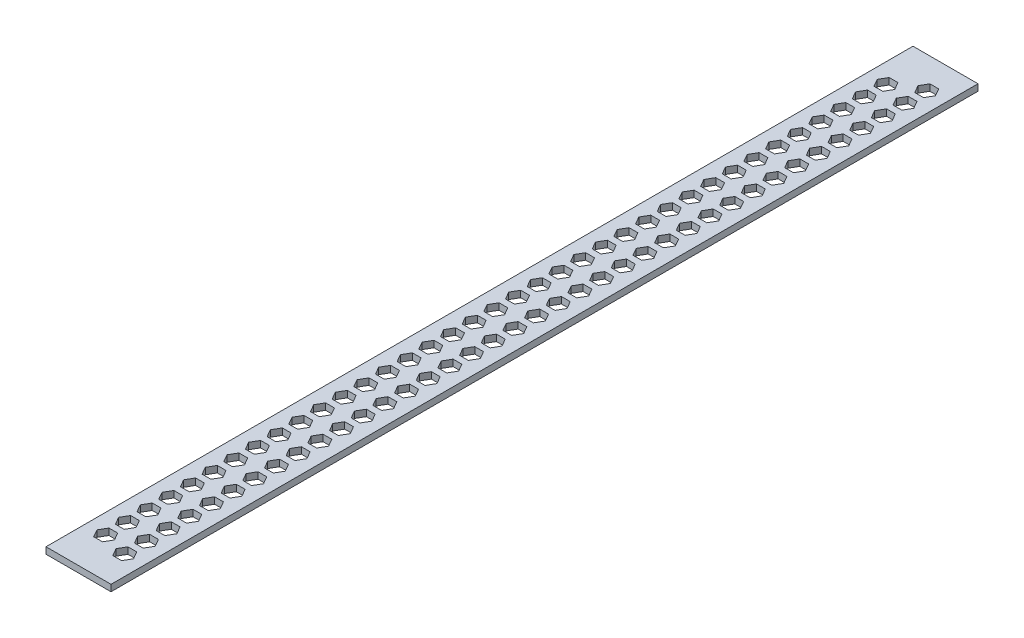
SolidWorks part; units mm, degrees
material "Balsa"
ref_plane "Front Plane" through (0, 0, 0) normal (0, 0, 1) x (1, 0, 0)
ref_plane "Top Plane" through (0, 0, 0) normal (0, 1, 0) x (1, 0, 0)
ref_plane "Right Plane" through (0, 0, 0) normal (1, 0, 0) x (0, 0, -1)
sketch "Sketch1" plane through (0, 0, 0) normal (0, 1, 0) x (1, 0, 0)
  line L1 (-36.5161, 312.7563) -> (-6.5161, 312.7563)
  line L2 (-36.5161, 312.7563) -> (-36.5161, -87.2437)
  line L3 (-36.5161, -87.2437) -> (-6.5161, -87.2437)
  line L4 (-6.5161, 312.7563) -> (-6.5161, -87.2437)
  line L5 (-36.5161, 312.7563) -> (-6.5161, -87.2437) construction
  line L6 (-36.5161, -87.2437) -> (-6.5161, 312.7563) construction
  point P0 (-21.5161, 112.7563)
  dimension "D1" = 400
  dimension "D2" = 30
extrude "Boss-Extrude1" add sketch "Sketch1" along normal blind 3
sketch "Sketch2" plane through (0, 0, 0) normal (0, -1, 0) x (-1, 0, 0)
  line L8 (11.5161, -71.8634) -> (13.5369, -75.3634)
  line L9 (13.5369, -75.3634) -> (17.5783, -75.3634)
  line L10 (17.5783, -75.3634) -> (19.599, -71.8634)
  line L11 (19.599, -71.8634) -> (17.5783, -68.3634)
  line L12 (17.5783, -68.3634) -> (13.5369, -68.3634)
  line L13 (13.5369, -68.3634) -> (11.5161, -71.8634)
  line L14 (6.5161, -87.2437) -> (6.5161, 312.7563) construction
  line L15 (13.5369, -58.3634) -> (11.5161, -61.8634)
  line L16 (11.5161, -61.8634) -> (13.5369, -65.3634)
  line L17 (13.5369, -65.3634) -> (17.5783, -65.3634)
  line L18 (17.5783, -65.3634) -> (19.599, -61.8634)
  line L19 (19.599, -61.8634) -> (17.5783, -58.3634)
  line L20 (17.5783, -58.3634) -> (13.5369, -58.3634)
  line L21 (25.454, -72.2437) -> (29.4954, -72.2437)
  line L22 (29.4954, -72.2437) -> (31.5161, -68.7437)
  line L23 (23.4332, -68.7437) -> (25.454, -72.2437)
  line L24 (25.454, -65.2437) -> (23.4332, -68.7437)
  line L25 (29.4954, -65.2437) -> (25.454, -65.2437)
  line L26 (31.5161, -68.7437) -> (29.4954, -65.2437)
  line L27 (13.5369, -48.3634) -> (11.5161, -51.8634)
  line L28 (11.5161, -51.8634) -> (13.5369, -55.3634)
  line L29 (13.5369, -55.3634) -> (17.5783, -55.3634)
  line L30 (17.5783, -55.3634) -> (19.599, -51.8634)
  line L31 (19.599, -51.8634) -> (17.5783, -48.3634)
  line L32 (17.5783, -48.3634) -> (13.5369, -48.3634)
  line L33 (25.454, -62.2437) -> (29.4954, -62.2437)
  line L34 (29.4954, -62.2437) -> (31.5161, -58.7437)
  line L35 (23.4332, -58.7437) -> (25.454, -62.2437)
  line L36 (25.454, -55.2437) -> (23.4332, -58.7437)
  line L37 (29.4954, -55.2437) -> (25.454, -55.2437)
  line L38 (31.5161, -58.7437) -> (29.4954, -55.2437)
  line L39 (13.5369, -38.3634) -> (11.5161, -41.8634)
  line L40 (11.5161, -41.8634) -> (13.5369, -45.3634)
  line L41 (13.5369, -45.3634) -> (17.5783, -45.3634)
  line L42 (17.5783, -45.3634) -> (19.599, -41.8634)
  line L43 (19.599, -41.8634) -> (17.5783, -38.3634)
  line L44 (17.5783, -38.3634) -> (13.5369, -38.3634)
  line L45 (25.454, -52.2437) -> (29.4954, -52.2437)
  line L46 (29.4954, -52.2437) -> (31.5161, -48.7437)
  line L47 (23.4332, -48.7437) -> (25.454, -52.2437)
  line L48 (25.454, -45.2437) -> (23.4332, -48.7437)
  line L49 (29.4954, -45.2437) -> (25.454, -45.2437)
  line L50 (31.5161, -48.7437) -> (29.4954, -45.2437)
  line L51 (13.5369, -28.3634) -> (11.5161, -31.8634)
  line L52 (11.5161, -31.8634) -> (13.5369, -35.3634)
  line L53 (13.5369, -35.3634) -> (17.5783, -35.3634)
  line L54 (17.5783, -35.3634) -> (19.599, -31.8634)
  line L55 (19.599, -31.8634) -> (17.5783, -28.3634)
  line L56 (17.5783, -28.3634) -> (13.5369, -28.3634)
  line L57 (25.454, -42.2437) -> (29.4954, -42.2437)
  line L58 (29.4954, -42.2437) -> (31.5161, -38.7437)
  line L59 (23.4332, -38.7437) -> (25.454, -42.2437)
  line L60 (25.454, -35.2437) -> (23.4332, -38.7437)
  line L61 (29.4954, -35.2437) -> (25.454, -35.2437)
  line L62 (31.5161, -38.7437) -> (29.4954, -35.2437)
  line L63 (13.5369, -18.3634) -> (11.5161, -21.8634)
  line L64 (11.5161, -21.8634) -> (13.5369, -25.3634)
  line L65 (13.5369, -25.3634) -> (17.5783, -25.3634)
  line L66 (17.5783, -25.3634) -> (19.599, -21.8634)
  line L67 (19.599, -21.8634) -> (17.5783, -18.3634)
  line L68 (17.5783, -18.3634) -> (13.5369, -18.3634)
  line L69 (25.454, -32.2437) -> (29.4954, -32.2437)
  line L70 (29.4954, -32.2437) -> (31.5161, -28.7437)
  line L71 (23.4332, -28.7437) -> (25.454, -32.2437)
  line L72 (25.454, -25.2437) -> (23.4332, -28.7437)
  line L73 (29.4954, -25.2437) -> (25.454, -25.2437)
  line L74 (31.5161, -28.7437) -> (29.4954, -25.2437)
  line L75 (13.5369, -8.3634) -> (11.5161, -11.8634)
  line L76 (11.5161, -11.8634) -> (13.5369, -15.3634)
  line L77 (13.5369, -15.3634) -> (17.5783, -15.3634)
  line L78 (17.5783, -15.3634) -> (19.599, -11.8634)
  line L79 (19.599, -11.8634) -> (17.5783, -8.3634)
  line L80 (17.5783, -8.3634) -> (13.5369, -8.3634)
  line L81 (25.454, -22.2437) -> (29.4954, -22.2437)
  line L82 (29.4954, -22.2437) -> (31.5161, -18.7437)
  line L83 (23.4332, -18.7437) -> (25.454, -22.2437)
  line L84 (25.454, -15.2437) -> (23.4332, -18.7437)
  line L85 (29.4954, -15.2437) -> (25.454, -15.2437)
  line L86 (31.5161, -18.7437) -> (29.4954, -15.2437)
  line L87 (13.5369, 1.6366) -> (11.5161, -1.8634)
  line L88 (11.5161, -1.8634) -> (13.5369, -5.3634)
  line L89 (13.5369, -5.3634) -> (17.5783, -5.3634)
  line L90 (17.5783, -5.3634) -> (19.599, -1.8634)
  line L91 (19.599, -1.8634) -> (17.5783, 1.6366)
  line L92 (17.5783, 1.6366) -> (13.5369, 1.6366)
  line L93 (25.454, -12.2437) -> (29.4954, -12.2437)
  line L94 (29.4954, -12.2437) -> (31.5161, -8.7437)
  line L95 (23.4332, -8.7437) -> (25.454, -12.2437)
  line L96 (25.454, -5.2437) -> (23.4332, -8.7437)
  line L97 (29.4954, -5.2437) -> (25.454, -5.2437)
  line L98 (31.5161, -8.7437) -> (29.4954, -5.2437)
  line L99 (13.5369, 11.6366) -> (11.5161, 8.1366)
  line L100 (11.5161, 8.1366) -> (13.5369, 4.6366)
  line L101 (13.5369, 4.6366) -> (17.5783, 4.6366)
  line L102 (17.5783, 4.6366) -> (19.599, 8.1366)
  line L103 (19.599, 8.1366) -> (17.5783, 11.6366)
  line L104 (17.5783, 11.6366) -> (13.5369, 11.6366)
  line L105 (25.454, -2.2437) -> (29.4954, -2.2437)
  line L106 (29.4954, -2.2437) -> (31.5161, 1.2563)
  line L107 (23.4332, 1.2563) -> (25.454, -2.2437)
  line L108 (25.454, 4.7563) -> (23.4332, 1.2563)
  line L109 (29.4954, 4.7563) -> (25.454, 4.7563)
  line L110 (31.5161, 1.2563) -> (29.4954, 4.7563)
  line L111 (13.5369, 21.6366) -> (11.5161, 18.1366)
  line L112 (11.5161, 18.1366) -> (13.5369, 14.6366)
  line L113 (13.5369, 14.6366) -> (17.5783, 14.6366)
  line L114 (17.5783, 14.6366) -> (19.599, 18.1366)
  line L115 (19.599, 18.1366) -> (17.5783, 21.6366)
  line L116 (17.5783, 21.6366) -> (13.5369, 21.6366)
  line L117 (25.454, 7.7563) -> (29.4954, 7.7563)
  line L118 (29.4954, 7.7563) -> (31.5161, 11.2563)
  line L119 (23.4332, 11.2563) -> (25.454, 7.7563)
  line L120 (25.454, 14.7563) -> (23.4332, 11.2563)
  line L121 (29.4954, 14.7563) -> (25.454, 14.7563)
  line L122 (31.5161, 11.2563) -> (29.4954, 14.7563)
  line L123 (13.5369, 31.6366) -> (11.5161, 28.1366)
  line L124 (11.5161, 28.1366) -> (13.5369, 24.6366)
  line L125 (13.5369, 24.6366) -> (17.5783, 24.6366)
  line L126 (17.5783, 24.6366) -> (19.599, 28.1366)
  line L127 (19.599, 28.1366) -> (17.5783, 31.6366)
  line L128 (17.5783, 31.6366) -> (13.5369, 31.6366)
  line L129 (25.454, 17.7563) -> (29.4954, 17.7563)
  line L130 (29.4954, 17.7563) -> (31.5161, 21.2563)
  line L131 (23.4332, 21.2563) -> (25.454, 17.7563)
  line L132 (25.454, 24.7563) -> (23.4332, 21.2563)
  line L133 (29.4954, 24.7563) -> (25.454, 24.7563)
  line L134 (31.5161, 21.2563) -> (29.4954, 24.7563)
  line L135 (13.5369, 41.6366) -> (11.5161, 38.1366)
  line L136 (11.5161, 38.1366) -> (13.5369, 34.6366)
  line L137 (13.5369, 34.6366) -> (17.5783, 34.6366)
  line L138 (17.5783, 34.6366) -> (19.599, 38.1366)
  line L139 (19.599, 38.1366) -> (17.5783, 41.6366)
  line L140 (17.5783, 41.6366) -> (13.5369, 41.6366)
  line L141 (25.454, 27.7563) -> (29.4954, 27.7563)
  line L142 (29.4954, 27.7563) -> (31.5161, 31.2563)
  line L143 (23.4332, 31.2563) -> (25.454, 27.7563)
  line L144 (25.454, 34.7563) -> (23.4332, 31.2563)
  line L145 (29.4954, 34.7563) -> (25.454, 34.7563)
  line L146 (31.5161, 31.2563) -> (29.4954, 34.7563)
  line L147 (13.5369, 51.6366) -> (11.5161, 48.1366)
  line L148 (11.5161, 48.1366) -> (13.5369, 44.6366)
  line L149 (13.5369, 44.6366) -> (17.5783, 44.6366)
  line L150 (17.5783, 44.6366) -> (19.599, 48.1366)
  line L151 (19.599, 48.1366) -> (17.5783, 51.6366)
  line L152 (17.5783, 51.6366) -> (13.5369, 51.6366)
  line L153 (25.454, 37.7563) -> (29.4954, 37.7563)
  line L154 (29.4954, 37.7563) -> (31.5161, 41.2563)
  line L155 (23.4332, 41.2563) -> (25.454, 37.7563)
  line L156 (25.454, 44.7563) -> (23.4332, 41.2563)
  line L157 (29.4954, 44.7563) -> (25.454, 44.7563)
  line L158 (31.5161, 41.2563) -> (29.4954, 44.7563)
  line L159 (13.5369, 61.6366) -> (11.5161, 58.1366)
  line L160 (11.5161, 58.1366) -> (13.5369, 54.6366)
  line L161 (13.5369, 54.6366) -> (17.5783, 54.6366)
  line L162 (17.5783, 54.6366) -> (19.599, 58.1366)
  line L163 (19.599, 58.1366) -> (17.5783, 61.6366)
  line L164 (17.5783, 61.6366) -> (13.5369, 61.6366)
  line L165 (25.454, 47.7563) -> (29.4954, 47.7563)
  line L166 (29.4954, 47.7563) -> (31.5161, 51.2563)
  line L167 (23.4332, 51.2563) -> (25.454, 47.7563)
  line L168 (25.454, 54.7563) -> (23.4332, 51.2563)
  line L169 (29.4954, 54.7563) -> (25.454, 54.7563)
  line L170 (31.5161, 51.2563) -> (29.4954, 54.7563)
  line L171 (13.5369, 71.6366) -> (11.5161, 68.1366)
  line L172 (11.5161, 68.1366) -> (13.5369, 64.6366)
  line L173 (13.5369, 64.6366) -> (17.5783, 64.6366)
  line L174 (17.5783, 64.6366) -> (19.599, 68.1366)
  line L175 (19.599, 68.1366) -> (17.5783, 71.6366)
  line L176 (17.5783, 71.6366) -> (13.5369, 71.6366)
  line L177 (25.454, 57.7563) -> (29.4954, 57.7563)
  line L178 (29.4954, 57.7563) -> (31.5161, 61.2563)
  line L179 (23.4332, 61.2563) -> (25.454, 57.7563)
  line L180 (25.454, 64.7563) -> (23.4332, 61.2563)
  line L181 (29.4954, 64.7563) -> (25.454, 64.7563)
  line L182 (31.5161, 61.2563) -> (29.4954, 64.7563)
  line L183 (13.5369, 81.6366) -> (11.5161, 78.1366)
  line L184 (11.5161, 78.1366) -> (13.5369, 74.6366)
  line L185 (13.5369, 74.6366) -> (17.5783, 74.6366)
  line L186 (17.5783, 74.6366) -> (19.599, 78.1366)
  line L187 (19.599, 78.1366) -> (17.5783, 81.6366)
  line L188 (17.5783, 81.6366) -> (13.5369, 81.6366)
  line L189 (25.454, 67.7563) -> (29.4954, 67.7563)
  line L190 (29.4954, 67.7563) -> (31.5161, 71.2563)
  line L191 (23.4332, 71.2563) -> (25.454, 67.7563)
  line L192 (25.454, 74.7563) -> (23.4332, 71.2563)
  line L193 (29.4954, 74.7563) -> (25.454, 74.7563)
  line L194 (31.5161, 71.2563) -> (29.4954, 74.7563)
  line L195 (13.5369, 91.6366) -> (11.5161, 88.1366)
  line L196 (11.5161, 88.1366) -> (13.5369, 84.6366)
  line L197 (13.5369, 84.6366) -> (17.5783, 84.6366)
  line L198 (17.5783, 84.6366) -> (19.599, 88.1366)
  line L199 (19.599, 88.1366) -> (17.5783, 91.6366)
  line L200 (17.5783, 91.6366) -> (13.5369, 91.6366)
  line L201 (25.454, 77.7563) -> (29.4954, 77.7563)
  line L202 (29.4954, 77.7563) -> (31.5161, 81.2563)
  line L203 (23.4332, 81.2563) -> (25.454, 77.7563)
  line L204 (25.454, 84.7563) -> (23.4332, 81.2563)
  line L205 (29.4954, 84.7563) -> (25.454, 84.7563)
  line L206 (31.5161, 81.2563) -> (29.4954, 84.7563)
  line L207 (13.5369, 101.6366) -> (11.5161, 98.1366)
  line L208 (11.5161, 98.1366) -> (13.5369, 94.6366)
  line L209 (13.5369, 94.6366) -> (17.5783, 94.6366)
  line L210 (17.5783, 94.6366) -> (19.599, 98.1366)
  line L211 (19.599, 98.1366) -> (17.5783, 101.6366)
  line L212 (17.5783, 101.6366) -> (13.5369, 101.6366)
  line L213 (25.454, 87.7563) -> (29.4954, 87.7563)
  line L214 (29.4954, 87.7563) -> (31.5161, 91.2563)
  line L215 (23.4332, 91.2563) -> (25.454, 87.7563)
  line L216 (25.454, 94.7563) -> (23.4332, 91.2563)
  line L217 (29.4954, 94.7563) -> (25.454, 94.7563)
  line L218 (31.5161, 91.2563) -> (29.4954, 94.7563)
  line L219 (13.5369, 111.6366) -> (11.5161, 108.1366)
  line L220 (11.5161, 108.1366) -> (13.5369, 104.6366)
  line L221 (13.5369, 104.6366) -> (17.5783, 104.6366)
  line L222 (17.5783, 104.6366) -> (19.599, 108.1366)
  line L223 (19.599, 108.1366) -> (17.5783, 111.6366)
  line L224 (17.5783, 111.6366) -> (13.5369, 111.6366)
  line L225 (25.454, 97.7563) -> (29.4954, 97.7563)
  line L226 (29.4954, 97.7563) -> (31.5161, 101.2563)
  line L227 (23.4332, 101.2563) -> (25.454, 97.7563)
  line L228 (25.454, 104.7563) -> (23.4332, 101.2563)
  line L229 (29.4954, 104.7563) -> (25.454, 104.7563)
  line L230 (31.5161, 101.2563) -> (29.4954, 104.7563)
  line L231 (13.5369, 121.6366) -> (11.5161, 118.1366)
  line L232 (11.5161, 118.1366) -> (13.5369, 114.6366)
  line L233 (13.5369, 114.6366) -> (17.5783, 114.6366)
  line L234 (17.5783, 114.6366) -> (19.599, 118.1366)
  line L235 (19.599, 118.1366) -> (17.5783, 121.6366)
  line L236 (17.5783, 121.6366) -> (13.5369, 121.6366)
  line L237 (25.454, 107.7563) -> (29.4954, 107.7563)
  line L238 (29.4954, 107.7563) -> (31.5161, 111.2563)
  line L239 (23.4332, 111.2563) -> (25.454, 107.7563)
  line L240 (25.454, 114.7563) -> (23.4332, 111.2563)
  line L241 (29.4954, 114.7563) -> (25.454, 114.7563)
  line L242 (31.5161, 111.2563) -> (29.4954, 114.7563)
  line L243 (13.5369, 131.6366) -> (11.5161, 128.1366)
  line L244 (11.5161, 128.1366) -> (13.5369, 124.6366)
  line L245 (13.5369, 124.6366) -> (17.5783, 124.6366)
  line L246 (17.5783, 124.6366) -> (19.599, 128.1366)
  line L247 (19.599, 128.1366) -> (17.5783, 131.6366)
  line L248 (17.5783, 131.6366) -> (13.5369, 131.6366)
  line L249 (25.454, 117.7563) -> (29.4954, 117.7563)
  line L250 (29.4954, 117.7563) -> (31.5161, 121.2563)
  line L251 (23.4332, 121.2563) -> (25.454, 117.7563)
  line L252 (25.454, 124.7563) -> (23.4332, 121.2563)
  line L253 (29.4954, 124.7563) -> (25.454, 124.7563)
  line L254 (31.5161, 121.2563) -> (29.4954, 124.7563)
  line L255 (13.5369, 141.6366) -> (11.5161, 138.1366)
  line L256 (11.5161, 138.1366) -> (13.5369, 134.6366)
  line L257 (13.5369, 134.6366) -> (17.5783, 134.6366)
  line L258 (17.5783, 134.6366) -> (19.599, 138.1366)
  line L259 (19.599, 138.1366) -> (17.5783, 141.6366)
  line L260 (17.5783, 141.6366) -> (13.5369, 141.6366)
  line L261 (25.454, 127.7563) -> (29.4954, 127.7563)
  line L262 (29.4954, 127.7563) -> (31.5161, 131.2563)
  line L263 (23.4332, 131.2563) -> (25.454, 127.7563)
  line L264 (25.454, 134.7563) -> (23.4332, 131.2563)
  line L265 (29.4954, 134.7563) -> (25.454, 134.7563)
  line L266 (31.5161, 131.2563) -> (29.4954, 134.7563)
  line L267 (13.5369, 151.6366) -> (11.5161, 148.1366)
  line L268 (11.5161, 148.1366) -> (13.5369, 144.6366)
  line L269 (13.5369, 144.6366) -> (17.5783, 144.6366)
  line L270 (17.5783, 144.6366) -> (19.599, 148.1366)
  line L271 (19.599, 148.1366) -> (17.5783, 151.6366)
  line L272 (17.5783, 151.6366) -> (13.5369, 151.6366)
  line L273 (25.454, 137.7563) -> (29.4954, 137.7563)
  line L274 (29.4954, 137.7563) -> (31.5161, 141.2563)
  line L275 (23.4332, 141.2563) -> (25.454, 137.7563)
  line L276 (25.454, 144.7563) -> (23.4332, 141.2563)
  line L277 (29.4954, 144.7563) -> (25.454, 144.7563)
  line L278 (31.5161, 141.2563) -> (29.4954, 144.7563)
  line L279 (13.5369, 161.6366) -> (11.5161, 158.1366)
  line L280 (11.5161, 158.1366) -> (13.5369, 154.6366)
  line L281 (13.5369, 154.6366) -> (17.5783, 154.6366)
  line L282 (17.5783, 154.6366) -> (19.599, 158.1366)
  line L283 (19.599, 158.1366) -> (17.5783, 161.6366)
  line L284 (17.5783, 161.6366) -> (13.5369, 161.6366)
  line L285 (25.454, 147.7563) -> (29.4954, 147.7563)
  line L286 (29.4954, 147.7563) -> (31.5161, 151.2563)
  line L287 (23.4332, 151.2563) -> (25.454, 147.7563)
  line L288 (25.454, 154.7563) -> (23.4332, 151.2563)
  line L289 (29.4954, 154.7563) -> (25.454, 154.7563)
  line L290 (31.5161, 151.2563) -> (29.4954, 154.7563)
  line L291 (13.5369, 171.6366) -> (11.5161, 168.1366)
  line L292 (11.5161, 168.1366) -> (13.5369, 164.6366)
  line L293 (13.5369, 164.6366) -> (17.5783, 164.6366)
  line L294 (17.5783, 164.6366) -> (19.599, 168.1366)
  line L295 (19.599, 168.1366) -> (17.5783, 171.6366)
  line L296 (17.5783, 171.6366) -> (13.5369, 171.6366)
  line L297 (25.454, 157.7563) -> (29.4954, 157.7563)
  line L298 (29.4954, 157.7563) -> (31.5161, 161.2563)
  line L299 (23.4332, 161.2563) -> (25.454, 157.7563)
  line L300 (25.454, 164.7563) -> (23.4332, 161.2563)
  line L301 (29.4954, 164.7563) -> (25.454, 164.7563)
  line L302 (31.5161, 161.2563) -> (29.4954, 164.7563)
  line L303 (13.5369, 181.6366) -> (11.5161, 178.1366)
  line L304 (11.5161, 178.1366) -> (13.5369, 174.6366)
  line L305 (13.5369, 174.6366) -> (17.5783, 174.6366)
  line L306 (17.5783, 174.6366) -> (19.599, 178.1366)
  line L307 (19.599, 178.1366) -> (17.5783, 181.6366)
  line L308 (17.5783, 181.6366) -> (13.5369, 181.6366)
  line L309 (25.454, 167.7563) -> (29.4954, 167.7563)
  line L310 (29.4954, 167.7563) -> (31.5161, 171.2563)
  line L311 (23.4332, 171.2563) -> (25.454, 167.7563)
  line L312 (25.454, 174.7563) -> (23.4332, 171.2563)
  line L313 (29.4954, 174.7563) -> (25.454, 174.7563)
  line L314 (31.5161, 171.2563) -> (29.4954, 174.7563)
  line L315 (13.5369, 191.6366) -> (11.5161, 188.1366)
  line L316 (11.5161, 188.1366) -> (13.5369, 184.6366)
  line L317 (13.5369, 184.6366) -> (17.5783, 184.6366)
  line L318 (17.5783, 184.6366) -> (19.599, 188.1366)
  line L319 (19.599, 188.1366) -> (17.5783, 191.6366)
  line L320 (17.5783, 191.6366) -> (13.5369, 191.6366)
  line L321 (25.454, 177.7563) -> (29.4954, 177.7563)
  line L322 (29.4954, 177.7563) -> (31.5161, 181.2563)
  line L323 (23.4332, 181.2563) -> (25.454, 177.7563)
  line L324 (25.454, 184.7563) -> (23.4332, 181.2563)
  line L325 (29.4954, 184.7563) -> (25.454, 184.7563)
  line L326 (31.5161, 181.2563) -> (29.4954, 184.7563)
  line L327 (13.5369, 201.6366) -> (11.5161, 198.1366)
  line L328 (11.5161, 198.1366) -> (13.5369, 194.6366)
  line L329 (13.5369, 194.6366) -> (17.5783, 194.6366)
  line L330 (17.5783, 194.6366) -> (19.599, 198.1366)
  line L331 (19.599, 198.1366) -> (17.5783, 201.6366)
  line L332 (17.5783, 201.6366) -> (13.5369, 201.6366)
  line L333 (25.454, 187.7563) -> (29.4954, 187.7563)
  line L334 (29.4954, 187.7563) -> (31.5161, 191.2563)
  line L335 (23.4332, 191.2563) -> (25.454, 187.7563)
  line L336 (25.454, 194.7563) -> (23.4332, 191.2563)
  line L337 (29.4954, 194.7563) -> (25.454, 194.7563)
  line L338 (31.5161, 191.2563) -> (29.4954, 194.7563)
  line L339 (13.5369, 211.6366) -> (11.5161, 208.1366)
  line L340 (11.5161, 208.1366) -> (13.5369, 204.6366)
  line L341 (13.5369, 204.6366) -> (17.5783, 204.6366)
  line L342 (17.5783, 204.6366) -> (19.599, 208.1366)
  line L343 (19.599, 208.1366) -> (17.5783, 211.6366)
  line L344 (17.5783, 211.6366) -> (13.5369, 211.6366)
  line L345 (25.454, 197.7563) -> (29.4954, 197.7563)
  line L346 (29.4954, 197.7563) -> (31.5161, 201.2563)
  line L347 (23.4332, 201.2563) -> (25.454, 197.7563)
  line L348 (25.454, 204.7563) -> (23.4332, 201.2563)
  line L349 (29.4954, 204.7563) -> (25.454, 204.7563)
  line L350 (31.5161, 201.2563) -> (29.4954, 204.7563)
  line L351 (13.5369, 221.6366) -> (11.5161, 218.1366)
  line L352 (11.5161, 218.1366) -> (13.5369, 214.6366)
  line L353 (13.5369, 214.6366) -> (17.5783, 214.6366)
  line L354 (17.5783, 214.6366) -> (19.599, 218.1366)
  line L355 (19.599, 218.1366) -> (17.5783, 221.6366)
  line L356 (17.5783, 221.6366) -> (13.5369, 221.6366)
  line L357 (25.454, 207.7563) -> (29.4954, 207.7563)
  line L358 (29.4954, 207.7563) -> (31.5161, 211.2563)
  line L359 (23.4332, 211.2563) -> (25.454, 207.7563)
  line L360 (25.454, 214.7563) -> (23.4332, 211.2563)
  line L361 (29.4954, 214.7563) -> (25.454, 214.7563)
  line L362 (31.5161, 211.2563) -> (29.4954, 214.7563)
  line L363 (13.5369, 231.6366) -> (11.5161, 228.1366)
  line L364 (11.5161, 228.1366) -> (13.5369, 224.6366)
  line L365 (13.5369, 224.6366) -> (17.5783, 224.6366)
  line L366 (17.5783, 224.6366) -> (19.599, 228.1366)
  line L367 (19.599, 228.1366) -> (17.5783, 231.6366)
  line L368 (17.5783, 231.6366) -> (13.5369, 231.6366)
  line L369 (25.454, 217.7563) -> (29.4954, 217.7563)
  line L370 (29.4954, 217.7563) -> (31.5161, 221.2563)
  line L371 (23.4332, 221.2563) -> (25.454, 217.7563)
  line L372 (25.454, 224.7563) -> (23.4332, 221.2563)
  line L373 (29.4954, 224.7563) -> (25.454, 224.7563)
  line L374 (31.5161, 221.2563) -> (29.4954, 224.7563)
  line L375 (13.5369, 241.6366) -> (11.5161, 238.1366)
  line L376 (11.5161, 238.1366) -> (13.5369, 234.6366)
  line L377 (13.5369, 234.6366) -> (17.5783, 234.6366)
  line L378 (17.5783, 234.6366) -> (19.599, 238.1366)
  line L379 (19.599, 238.1366) -> (17.5783, 241.6366)
  line L380 (17.5783, 241.6366) -> (13.5369, 241.6366)
  line L381 (25.454, 227.7563) -> (29.4954, 227.7563)
  line L382 (29.4954, 227.7563) -> (31.5161, 231.2563)
  line L383 (23.4332, 231.2563) -> (25.454, 227.7563)
  line L384 (25.454, 234.7563) -> (23.4332, 231.2563)
  line L385 (29.4954, 234.7563) -> (25.454, 234.7563)
  line L386 (31.5161, 231.2563) -> (29.4954, 234.7563)
  line L387 (13.5369, 251.6366) -> (11.5161, 248.1366)
  line L388 (11.5161, 248.1366) -> (13.5369, 244.6366)
  line L389 (13.5369, 244.6366) -> (17.5783, 244.6366)
  line L390 (17.5783, 244.6366) -> (19.599, 248.1366)
  line L391 (19.599, 248.1366) -> (17.5783, 251.6366)
  line L392 (17.5783, 251.6366) -> (13.5369, 251.6366)
  line L393 (25.454, 237.7563) -> (29.4954, 237.7563)
  line L394 (29.4954, 237.7563) -> (31.5161, 241.2563)
  line L395 (23.4332, 241.2563) -> (25.454, 237.7563)
  line L396 (25.454, 244.7563) -> (23.4332, 241.2563)
  line L397 (29.4954, 244.7563) -> (25.454, 244.7563)
  line L398 (31.5161, 241.2563) -> (29.4954, 244.7563)
  line L399 (13.5369, 261.6366) -> (11.5161, 258.1366)
  line L400 (11.5161, 258.1366) -> (13.5369, 254.6366)
  line L401 (13.5369, 254.6366) -> (17.5783, 254.6366)
  line L402 (17.5783, 254.6366) -> (19.599, 258.1366)
  line L403 (19.599, 258.1366) -> (17.5783, 261.6366)
  line L404 (17.5783, 261.6366) -> (13.5369, 261.6366)
  line L405 (25.454, 247.7563) -> (29.4954, 247.7563)
  line L406 (29.4954, 247.7563) -> (31.5161, 251.2563)
  line L407 (23.4332, 251.2563) -> (25.454, 247.7563)
  line L408 (25.454, 254.7563) -> (23.4332, 251.2563)
  line L409 (29.4954, 254.7563) -> (25.454, 254.7563)
  line L410 (31.5161, 251.2563) -> (29.4954, 254.7563)
  line L411 (13.5369, 271.6366) -> (11.5161, 268.1366)
  line L412 (11.5161, 268.1366) -> (13.5369, 264.6366)
  line L413 (13.5369, 264.6366) -> (17.5783, 264.6366)
  line L414 (17.5783, 264.6366) -> (19.599, 268.1366)
  line L415 (19.599, 268.1366) -> (17.5783, 271.6366)
  line L416 (17.5783, 271.6366) -> (13.5369, 271.6366)
  line L417 (25.454, 257.7563) -> (29.4954, 257.7563)
  line L418 (29.4954, 257.7563) -> (31.5161, 261.2563)
  line L419 (23.4332, 261.2563) -> (25.454, 257.7563)
  line L420 (25.454, 264.7563) -> (23.4332, 261.2563)
  line L421 (29.4954, 264.7563) -> (25.454, 264.7563)
  line L422 (31.5161, 261.2563) -> (29.4954, 264.7563)
  line L423 (13.5369, 281.6366) -> (11.5161, 278.1366)
  line L424 (11.5161, 278.1366) -> (13.5369, 274.6366)
  line L425 (13.5369, 274.6366) -> (17.5783, 274.6366)
  line L426 (17.5783, 274.6366) -> (19.599, 278.1366)
  line L427 (19.599, 278.1366) -> (17.5783, 281.6366)
  line L428 (17.5783, 281.6366) -> (13.5369, 281.6366)
  line L429 (25.454, 267.7563) -> (29.4954, 267.7563)
  line L430 (29.4954, 267.7563) -> (31.5161, 271.2563)
  line L431 (23.4332, 271.2563) -> (25.454, 267.7563)
  line L432 (25.454, 274.7563) -> (23.4332, 271.2563)
  line L433 (29.4954, 274.7563) -> (25.454, 274.7563)
  line L434 (31.5161, 271.2563) -> (29.4954, 274.7563)
  line L435 (13.5369, 291.6366) -> (11.5161, 288.1366)
  line L436 (11.5161, 288.1366) -> (13.5369, 284.6366)
  line L437 (13.5369, 284.6366) -> (17.5783, 284.6366)
  line L438 (17.5783, 284.6366) -> (19.599, 288.1366)
  line L439 (19.599, 288.1366) -> (17.5783, 291.6366)
  line L440 (17.5783, 291.6366) -> (13.5369, 291.6366)
  line L441 (25.454, 277.7563) -> (29.4954, 277.7563)
  line L442 (29.4954, 277.7563) -> (31.5161, 281.2563)
  line L443 (23.4332, 281.2563) -> (25.454, 277.7563)
  line L444 (25.454, 284.7563) -> (23.4332, 281.2563)
  line L445 (29.4954, 284.7563) -> (25.454, 284.7563)
  line L446 (31.5161, 281.2563) -> (29.4954, 284.7563)
  line L447 (13.5369, 301.6366) -> (11.5161, 298.1366)
  line L448 (11.5161, 298.1366) -> (13.5369, 294.6366)
  line L449 (13.5369, 294.6366) -> (17.5783, 294.6366)
  line L450 (17.5783, 294.6366) -> (19.599, 298.1366)
  line L451 (19.599, 298.1366) -> (17.5783, 301.6366)
  line L452 (17.5783, 301.6366) -> (13.5369, 301.6366)
  line L453 (25.454, 287.7563) -> (29.4954, 287.7563)
  line L454 (29.4954, 287.7563) -> (31.5161, 291.2563)
  line L455 (23.4332, 291.2563) -> (25.454, 287.7563)
  line L456 (25.454, 294.7563) -> (23.4332, 291.2563)
  line L457 (29.4954, 294.7563) -> (25.454, 294.7563)
  line L458 (31.5161, 291.2563) -> (29.4954, 294.7563)
  circle A1 centre (15.5576, -71.8634) radius 3.5 construction
  circle A2 centre (15.5576, -61.8634) radius 3.5 construction
  circle A3 centre (27.4747, -68.7437) radius 3.5 construction
  circle A4 centre (15.5576, -51.8634) radius 3.5 construction
  circle A5 centre (27.4747, -58.7437) radius 3.5 construction
  circle A6 centre (15.5576, -41.8634) radius 3.5 construction
  circle A7 centre (27.4747, -48.7437) radius 3.5 construction
  circle A8 centre (15.5576, -31.8634) radius 3.5 construction
  circle A9 centre (27.4747, -38.7437) radius 3.5 construction
  circle A10 centre (15.5576, -21.8634) radius 3.5 construction
  circle A11 centre (27.4747, -28.7437) radius 3.5 construction
  circle A12 centre (15.5576, -11.8634) radius 3.5 construction
  circle A13 centre (27.4747, -18.7437) radius 3.5 construction
  circle A14 centre (15.5576, -1.8634) radius 3.5 construction
  circle A15 centre (27.4747, -8.7437) radius 3.5 construction
  circle A16 centre (15.5576, 8.1366) radius 3.5 construction
  circle A17 centre (27.4747, 1.2563) radius 3.5 construction
  circle A18 centre (15.5576, 18.1366) radius 3.5 construction
  circle A19 centre (27.4747, 11.2563) radius 3.5 construction
  circle A20 centre (15.5576, 28.1366) radius 3.5 construction
  circle A21 centre (27.4747, 21.2563) radius 3.5 construction
  circle A22 centre (15.5576, 38.1366) radius 3.5 construction
  circle A23 centre (27.4747, 31.2563) radius 3.5 construction
  circle A24 centre (15.5576, 48.1366) radius 3.5 construction
  circle A25 centre (27.4747, 41.2563) radius 3.5 construction
  circle A26 centre (15.5576, 58.1366) radius 3.5 construction
  circle A27 centre (27.4747, 51.2563) radius 3.5 construction
  circle A28 centre (15.5576, 68.1366) radius 3.5 construction
  circle A29 centre (27.4747, 61.2563) radius 3.5 construction
  circle A30 centre (15.5576, 78.1366) radius 3.5 construction
  circle A31 centre (27.4747, 71.2563) radius 3.5 construction
  circle A32 centre (15.5576, 88.1366) radius 3.5 construction
  circle A33 centre (27.4747, 81.2563) radius 3.5 construction
  circle A34 centre (15.5576, 98.1366) radius 3.5 construction
  circle A35 centre (27.4747, 91.2563) radius 3.5 construction
  circle A36 centre (15.5576, 108.1366) radius 3.5 construction
  circle A37 centre (27.4747, 101.2563) radius 3.5 construction
  circle A38 centre (15.5576, 118.1366) radius 3.5 construction
  circle A39 centre (27.4747, 111.2563) radius 3.5 construction
  circle A40 centre (15.5576, 128.1366) radius 3.5 construction
  circle A41 centre (27.4747, 121.2563) radius 3.5 construction
  circle A42 centre (15.5576, 138.1366) radius 3.5 construction
  circle A43 centre (27.4747, 131.2563) radius 3.5 construction
  circle A44 centre (15.5576, 148.1366) radius 3.5 construction
  circle A45 centre (27.4747, 141.2563) radius 3.5 construction
  circle A46 centre (15.5576, 158.1366) radius 3.5 construction
  circle A47 centre (27.4747, 151.2563) radius 3.5 construction
  circle A48 centre (15.5576, 168.1366) radius 3.5 construction
  circle A49 centre (27.4747, 161.2563) radius 3.5 construction
  circle A50 centre (15.5576, 178.1366) radius 3.5 construction
  circle A51 centre (27.4747, 171.2563) radius 3.5 construction
  circle A52 centre (15.5576, 188.1366) radius 3.5 construction
  circle A53 centre (27.4747, 181.2563) radius 3.5 construction
  circle A54 centre (15.5576, 198.1366) radius 3.5 construction
  circle A55 centre (27.4747, 191.2563) radius 3.5 construction
  circle A56 centre (15.5576, 208.1366) radius 3.5 construction
  circle A57 centre (27.4747, 201.2563) radius 3.5 construction
  circle A58 centre (15.5576, 218.1366) radius 3.5 construction
  circle A59 centre (27.4747, 211.2563) radius 3.5 construction
  circle A60 centre (15.5576, 228.1366) radius 3.5 construction
  circle A61 centre (27.4747, 221.2563) radius 3.5 construction
  circle A62 centre (15.5576, 238.1366) radius 3.5 construction
  circle A63 centre (27.4747, 231.2563) radius 3.5 construction
  circle A64 centre (15.5576, 248.1366) radius 3.5 construction
  circle A65 centre (27.4747, 241.2563) radius 3.5 construction
  circle A66 centre (15.5576, 258.1366) radius 3.5 construction
  circle A67 centre (27.4747, 251.2563) radius 3.5 construction
  circle A68 centre (15.5576, 268.1366) radius 3.5 construction
  circle A69 centre (27.4747, 261.2563) radius 3.5 construction
  circle A70 centre (15.5576, 278.1366) radius 3.5 construction
  circle A71 centre (27.4747, 271.2563) radius 3.5 construction
  circle A72 centre (15.5576, 288.1366) radius 3.5 construction
  circle A73 centre (27.4747, 281.2563) radius 3.5 construction
  circle A74 centre (15.5576, 298.1366) radius 3.5 construction
  circle A75 centre (27.4747, 291.2563) radius 3.5 construction
  dimension "D5" = 5
  dimension "D6" = 38
extrude "Cut-Extrude1" cut sketch "Sketch2" against normal through all
